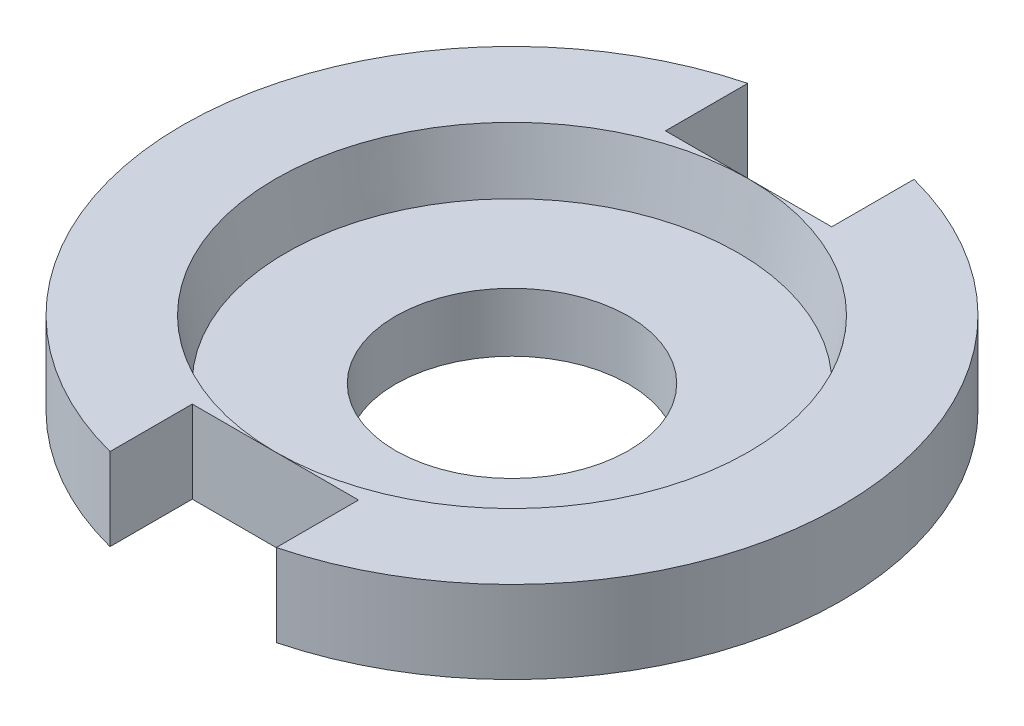
SolidWorks part; units mm, degrees
ref_plane "Спереди" through (0, 0, 0) normal (0, 0, 1) x (1, 0, 0)
ref_plane "Сверху" through (0, 0, 0) normal (0, 1, 0) x (1, 0, 0)
ref_plane "Справа" through (0, 0, 0) normal (1, 0, 0) x (0, 0, -1)
sketch "Sketch1" plane through (0, 0, 0) normal (0, 1, 0) x (1, 0, 0)
  circle A0 centre (0, 0) radius 28
extrude "Boss-Extrude1" add sketch "Sketch1" along normal blind 5
sketch "Sketch2" plane through (0, 5, 0) normal (0, 1, 0) x (1, 0, 0)
  circle A0 centre (0, 0) radius 20.1
extrude "Cut-Extrude1" cut sketch "Sketch2" against normal blind 5 draft 10
sketch "Sketch3" plane through (0, 0, 0) normal (0, -1, 0) x (1, 0, 0)
  circle A0 centre (0, 0) radius 28
extrude "Boss-Extrude2" add sketch "Sketch3" along normal blind 2
sketch "Sketch4" plane through (0, -2, 0) normal (0, -1, 0) x (-1, 0, 0)
  circle A0 centre (0, 0) radius 9.9
  circle A1 centre (0, 0) radius 14.9
extrude "Boss-Extrude3" add sketch "Sketch4" along normal blind 3
sketch "Sketch5" plane through (0, -2, 0) normal (0, -1, 0) x (-1, 0, 0)
  circle A0 centre (0, 0) radius 9.9
extrude "Cut-Extrude2" cut sketch "Sketch5" against normal through all
sketch "Sketch6" plane through (0, -2, 0) normal (0, -1, 0) x (1, 0, 0)
  line L1 (7.063, -30.04) -> (7.063, -20.1052)
  line L2 (-7.063, -30.04) -> (-7.063, -20.1052)
  line L3 (7.063, 29.9954) -> (-7.063, 29.9954)
  line L4 (7.063, 20.1052) -> (-7.063, 20.1052)
  line L5 (-7.063, 20.1052) -> (-7.063, 29.9954)
  line L7 (7.063, -30.04) -> (-7.063, -30.04)
  line L8 (7.063, -20.1052) -> (-7.063, -20.1052)
  line L9 (7.063, 20.1052) -> (7.063, 29.9954)
  line L10 (-7.063, 20.1052) -> (-7.063, 29.9954)
  circle M6 centre (0, 0) radius 28
extrude "Cut-Extrude3" cut sketch "Sketch6" against normal through all contours L4 L9 L3 L5 M6 | L1 L8 L2 L7 M6
